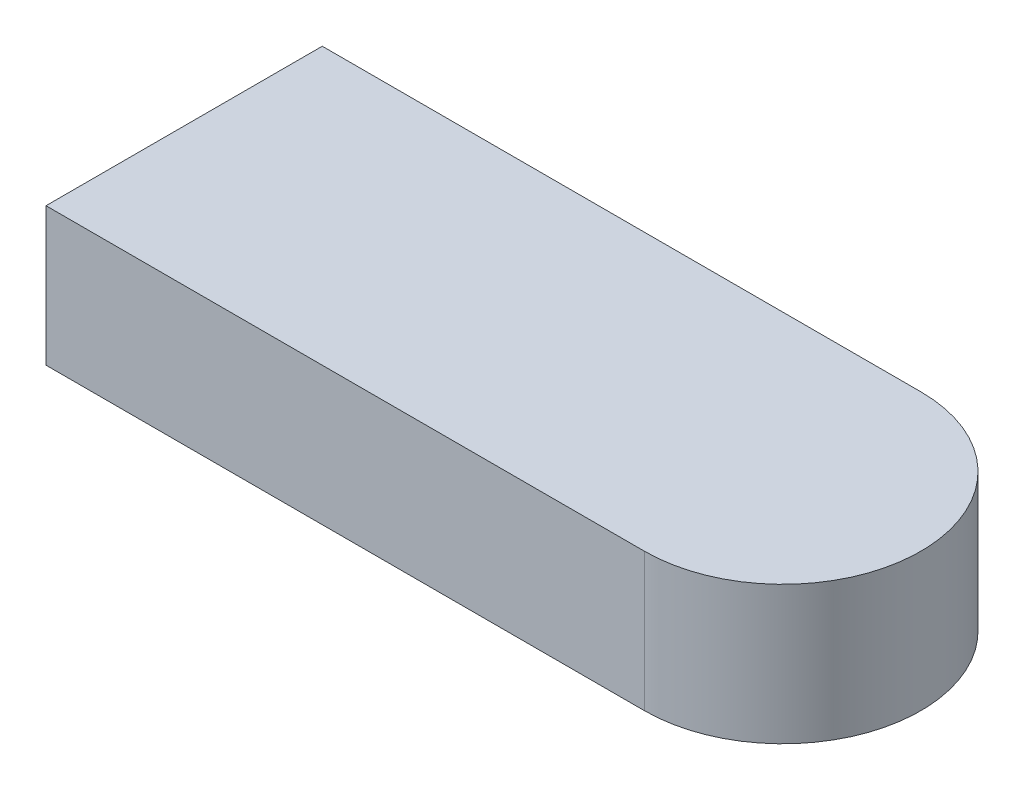
SolidWorks part; units mm, degrees
ref_plane "Front Plane" through (0, 0, 0) normal (0, 0, 1) x (1, 0, 0)
ref_plane "Top Plane" through (0, 0, 0) normal (0, 1, 0) x (1, 0, 0)
ref_plane "Right Plane" through (0, 0, 0) normal (1, 0, 0) x (0, 0, -1)
sketch "Sketch2" plane through (0, 0, 0) normal (0, 1, 0) x (1, 0, 0)
  line L1 (-40, 15) -> (40, 15)
  line L2 (-40, 15) -> (-40, -15)
  line L3 (-40, -15) -> (40, -15)
  line L4 (40, 15) -> (40, -15)
  dimension "D1" = 40
  dimension "D2" = 15
  dimension "D3" = 30
  dimension "D4" = 80
extrude "Boss-Extrude1" add sketch "Sketch2" along normal blind 15
sketch "Sketch4" plane through (0, 15, 0) normal (0, 1, 0) x (1, 0, 0)
  line L6 (40, -15) -> (40, 15) construction
  line L7 (25, 15) -> (40, 15)
  line L8 (40, 15) -> (40, 0)
  arc A1 (40, 0) -> (25, 15) centre (25, 0) ccw
  dimension "D1" = 15
extrude "Cut-Extrude4" cut sketch "Sketch4" against normal through all
sketch "Sketch5" plane through (0, 15, 0) normal (0, 1, 0) x (1, 0, 0)
  line L0 (40, 0) -> (40, -15)
  line L1 (40, -15) -> (25, -15)
  arc A0 (40, 0) -> (25, -15) centre (25, 0) cw
  dimension "D1" = 15
extrude "Cut-Extrude5" cut sketch "Sketch5" against normal through all
